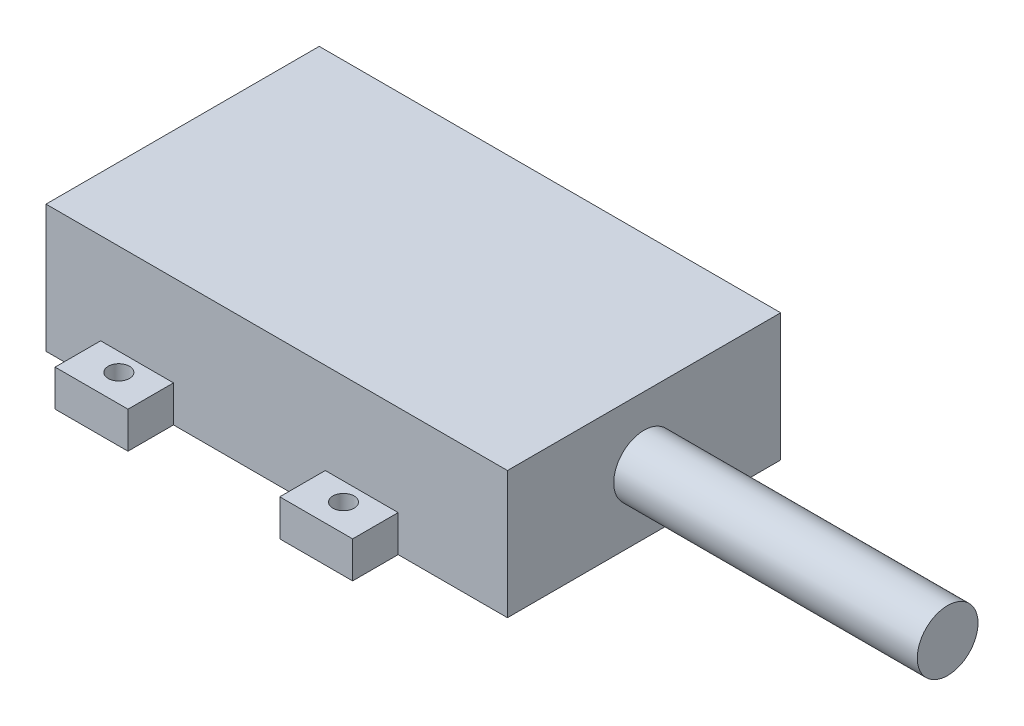
SolidWorks part; units mm, degrees
ref_plane "前视基准面" through (0, 0, 0) normal (0, 0, 1) x (1, 0, 0)
ref_plane "上视基准面" through (0, 0, 0) normal (0, 1, 0) x (1, 0, 0)
ref_plane "右视基准面" through (0, 0, 0) normal (1, 0, 0) x (0, 0, -1)
sketch "草图1" plane through (0, 0, 0) normal (0, 1, 0) x (1, 0, 0)
  line L1 (-38, 22.5) -> (38, 22.5)
  line L2 (-38, 22.5) -> (-38, -22.5)
  line L3 (-38, -22.5) -> (38, -22.5)
  line L4 (38, 22.5) -> (38, -22.5)
  line L5 (-38, 22.5) -> (38, -22.5) construction
  line L6 (-38, -22.5) -> (38, 22.5) construction
  point P0 (0, 0)
  dimension "D1" = 45
  dimension "D2" = 76
extrude "凸台-拉伸1" add sketch "草图1" along normal blind 21
sketch "草图2" plane through (0, 0, 0) normal (0, 1, 0) x (1, 0, 0)
  line L0 (-38, -22.5) -> (-23, -22.5) construction
  line L1 (-38, -22.5) -> (38, -22.5) construction
  line L2 (-23, -22.5) -> (14, -22.5) construction
  line L3 (-23, -22.5) -> (-23, -30) construction
  line L4 (-29, -15) -> (-17, -15)
  line L5 (-29, -15) -> (-29, -30)
  line L6 (-29, -30) -> (-17, -30)
  line L7 (-17, -15) -> (-17, -30)
  line L8 (-29, -15) -> (-17, -30) construction
  line L9 (-29, -30) -> (-17, -15) construction
  line L10 (8, -15) -> (20, -15)
  line L11 (8, -15) -> (8, -30)
  line L12 (8, -30) -> (20, -30)
  line L13 (20, -15) -> (20, -30)
  line L14 (8, -15) -> (20, -30) construction
  line L15 (8, -30) -> (20, -15) construction
  line L16 (14, -22.5) -> (14, -30) construction
  line L17 (-38, 0) -> (38, 0) construction
  line L18 (-38, 22.5) -> (-38, -22.5) construction
  line L19 (38, -22.5) -> (38, 22.5) construction
  line L20 (8, 30) -> (20, 30)
  line L21 (20, 15) -> (20, 30)
  line L22 (8, 15) -> (20, 15)
  line L23 (8, 15) -> (8, 30)
  line L24 (-29, 30) -> (-17, 30)
  line L25 (-17, 15) -> (-17, 30)
  line L26 (-29, 15) -> (-17, 15)
  line L27 (-29, 15) -> (-29, 30)
  circle A0 centre (-23, -25.5) radius 1.75
  circle A1 centre (14, -25.5) radius 1.75
  circle A2 centre (14, 25.5) radius 1.75
  circle A3 centre (-23, 25.5) radius 1.75
  dimension "D8" = 3.5
  dimension "D9" = 3.5
  dimension "D1" = 15
  dimension "D2" = 37
  dimension "D3" = 12
  dimension "D4" = 12
  dimension "D5" = 15
  dimension "D6" = 15
  dimension "D7" = 3
extrude "凸台-拉伸2" add sketch "草图2" along normal blind 6
ref_plane "基准面1" through (38, 0, 0) normal (1, 0, 0) x (0, 0, -1)
sketch "草图3" plane through (38, 0, 0) normal (1, 0, 0) x (0, 0, -1)
  line L0 (-22.5, 21) -> (22.5, 0) construction
  circle A0 centre (0, 10.5) radius 5
  dimension "D1" = 10
extrude "凸台-拉伸3" add sketch "草图3" along normal blind 50
